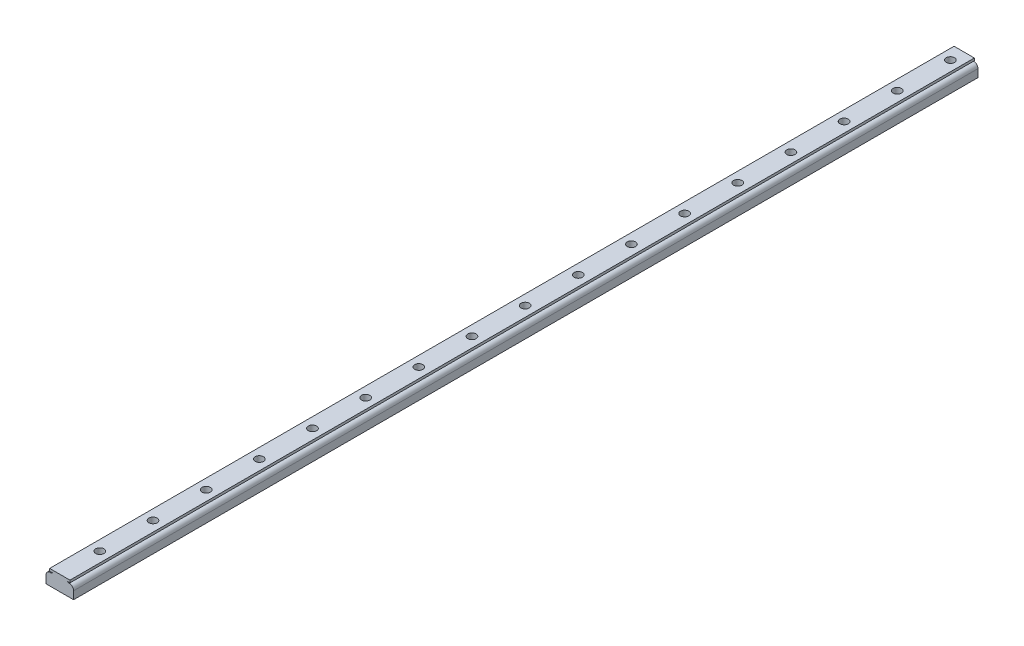
SolidWorks part; units mm, degrees
ref_plane "Alzado" through (0, 0, 0) normal (0, 0, 1) x (1, 0, 0)
ref_plane "Planta" through (0, 0, 0) normal (0, 1, 0) x (1, 0, 0)
ref_plane "Vista lateral" through (0, 0, 0) normal (1, 0, 0) x (0, 0, -1)
sketch "Croquis1" plane through (0, 0, 0) normal (0, 0, 1) x (1, 0, 0)
  line L0 (-10, 0) -> (-10, 5.6561)
  line L1 (-25, 0) -> (-10, 0) construction
  line L2 (-25, 0) -> (-25, 20) construction
  line L3 (-25, 20) -> (25, 20) construction
  line L4 (25, 0) -> (25, 20) construction
  line L5 (10, 0) -> (10, 5.6561)
  line L6 (-6.4615, 8.6073) -> (-5.2217, 9.2369)
  line L7 (-5.2217, 9.2369) -> (-7.3548, 9.2369)
  line L8 (-7.3548, 9.2369) -> (-7.3548, 11)
  line L9 (-7.3548, 11) -> (7.3548, 11)
  line L10 (0, 11) -> (0, 0) construction
  line L11 (6.4615, 8.6073) -> (5.2217, 9.2369)
  line L12 (5.2217, 9.2369) -> (7.3548, 9.2369)
  line L13 (7.3548, 9.2369) -> (7.3548, 11)
  line L14 (10, 0) -> (25, 0) construction
  line L15 (-10, 0) -> (0, 0)
  line L16 (0, 0) -> (10, 0)
  arc A0 (-10, 5.6561) -> (-6.4615, 8.6073) centre (-7, 5.6561) cw
  arc A1 (10, 5.6561) -> (6.4615, 8.6073) centre (7, 5.6561) ccw
  dimension "D3" = 3
  dimension "D1" = 50
  dimension "D2" = 20
  dimension "D4" = 15
  dimension "D5" = 11
extrude "Saliente-Extruir1" add sketch "Croquis1" along normal blind 655 contours L5 A1 L11 L12 L13 L9 L8 L7 L6 A0 L0 L15 L16
sketch "Croquis2" plane through (0, 11, 0) normal (0, 1, 0) x (1, 0, 0)
  line L0 (0, 0) -> (0, -10) construction
  line L1 (-7.3548, 0) -> (7.3548, 0) construction
  circle A0 centre (0, -10) radius 3
  circle A1 centre (0, -48.5) radius 3
  circle A2 centre (0, -87) radius 3
  circle A3 centre (0, -125.5) radius 3
  circle A4 centre (0, -164) radius 3
  circle A5 centre (0, -202.5) radius 3
  circle A6 centre (0, -241) radius 3
  circle A7 centre (0, -279.5) radius 3
  circle A8 centre (0, -318) radius 3
  circle A9 centre (0, -356.5) radius 3
  circle A10 centre (0, -395) radius 3
  circle A11 centre (0, -433.5) radius 3
  circle A12 centre (0, -472) radius 3
  circle A13 centre (0, -510.5) radius 3
  circle A14 centre (0, -549) radius 3
  circle A15 centre (0, -587.5) radius 3
  circle A16 centre (0, -626) radius 3
  dimension "D1" = 6
  dimension "D2" = 10
  dimension "D3" = 17
extrude "Cortar-Extruir1" cut sketch "Croquis2" against normal blind 12
